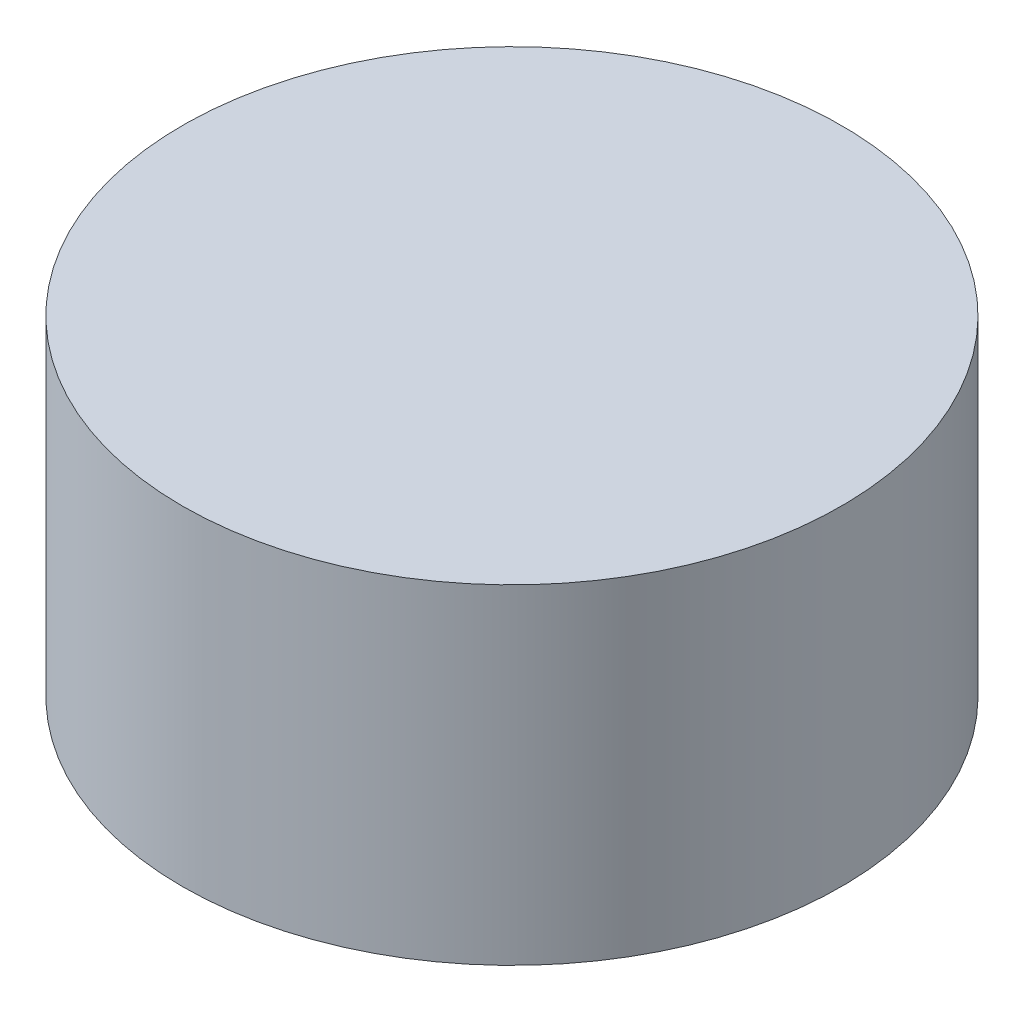
SolidWorks part; units mm, degrees
material "Titanium"
ref_plane "Front Plane" through (0, 0, 0) normal (0, 0, 1) x (1, 0, 0)
ref_plane "Top Plane" through (0, 0, 0) normal (0, 1, 0) x (1, 0, 0)
ref_plane "Right Plane" through (0, 0, 0) normal (1, 0, 0) x (0, 0, -1)
sketch "Sketch1" plane through (0, 0, 0) normal (0, 1, 0) x (1, 0, 0)
  circle A0 centre (0, 0) radius 5
  dimension "D1" = 10
extrude "Boss-Extrude1" add sketch "Sketch1" along normal blind 5 contours A0
